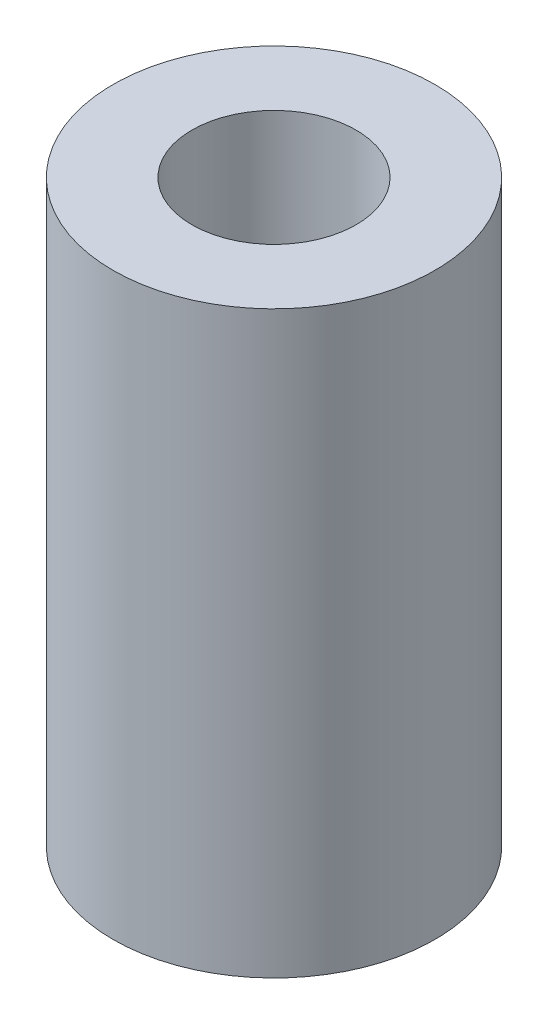
SolidWorks part; units mm, degrees
ref_plane "Front Plane" through (0, 0, 0) normal (0, 0, 1) x (1, 0, 0)
ref_plane "Top Plane" through (0, 0, 0) normal (0, 1, 0) x (1, 0, 0)
ref_plane "Right Plane" through (0, 0, 0) normal (1, 0, 0) x (0, 0, -1)
sketch "Sketch1" plane through (0, 0, 0) normal (0, 1, 0) x (1, 0, 0)
  circle A0 centre (0, 0) radius 6.35
  dimension "D1" = 12.7
extrude "Boss-Extrude1" add sketch "Sketch1" along normal blind 22.86
sketch "Sketch2" plane through (0, 0, 0) normal (0, -1, 0) x (1, 0, 0)
  circle A0 centre (0, 0) radius 3.048
  dimension "D1" = 6.096
extrude "Cut-Extrude1" cut sketch "Sketch2" against normal blind 8.636
sketch "Sketch3" plane through (0, 22.86, 0) normal (0, 1, 0) x (1, 0, 0)
  circle A0 centre (0, 0) radius 3.2385
  dimension "D1" = 6.477
extrude "Cut-Extrude2" cut sketch "Sketch3" against normal blind 10.16
